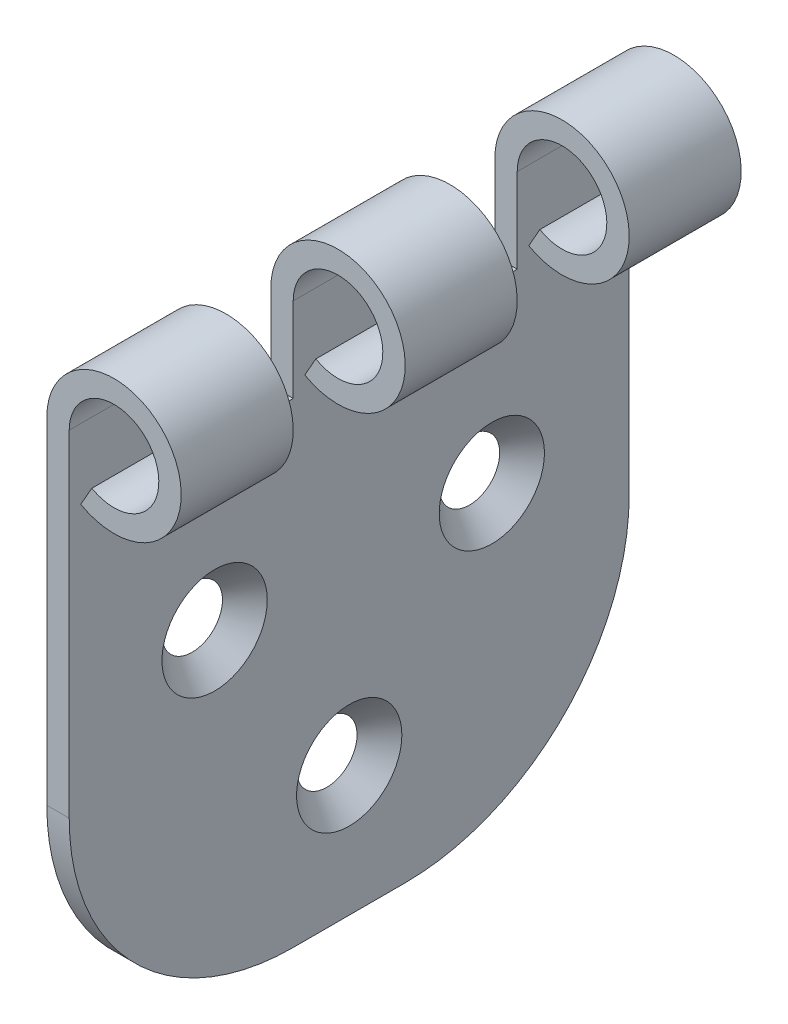
SolidWorks part; units mm, degrees
ref_plane "Front Plane" through (0, 0, 0) normal (0, 0, 1) x (1, 0, 0)
ref_plane "Top Plane" through (0, 0, 0) normal (0, 1, 0) x (1, 0, 0)
ref_plane "Right Plane" through (0, 0, 0) normal (1, 0, 0) x (0, 0, -1)
sketch "Sketch1" plane through (0, 0, 0) normal (0, 0, 1) x (1, 0, 0)
  line L0 (0, 0) -> (0, 50)
  line L1 (0, 50) -> (2, 50) construction
  line L2 (2, 50) -> (2, 0)
  line L3 (2, 0) -> (0, 0)
  line L4 (3.0328, 44.7851) -> (4.0218, 46.5234)
  arc A0 (3.0328, 44.7851) -> (0, 50) centre (6, 50) ccw
  arc A1 (4.0218, 46.5234) -> (2, 50) centre (6, 50) ccw
  dimension "D3" = 12
  dimension "D1" = 50
  dimension "D2" = 2
extrude "Boss-Extrude1" add sketch "Sketch1" along normal mid plane 50
sketch "Sketch2" plane through (2, 0, 0) normal (1, 0, 0) x (0, 0, -1)
  line L0 (-25, 0) -> (-25, 50) construction
  line L1 (-15, 63.0451) -> (-5, 63.0451)
  line L2 (-15, 63.0451) -> (-15, 42.4547)
  line L3 (-15, 42.4547) -> (-5, 42.4547)
  line L4 (-5, 63.0451) -> (-5, 42.4547)
  line L9 (5, 63.0451) -> (15, 63.0451)
  line L10 (5, 63.0451) -> (5, 42.4547)
  line L11 (5, 42.4547) -> (15, 42.4547)
  line L12 (15, 63.0451) -> (15, 42.4547)
  dimension "D1" = 10
  dimension "D2" = 10
  dimension "D3" = 10
  dimension "D4" = 10
extrude "Cut-Extrude1" cut sketch "Sketch2" along normal through all both and the other way through all
fillet "Fillet1" radius 20 2 edges at (1, 0, -25) (1, 0, 25)
hole_wizard "CSK for M4 Countersunk Flat Head Screw1" positions "Sketch3" profile "Sketch4" countersink size "M4" standard "ISO" end condition through all
sketch "Sketch3" plane through (2, 0, 0) normal (1, 0, 0) x (0, 0, -1)
  point P0 (0, 11.5875)
  point P2 (-12.0173, 28.0398)
  point P4 (12.7326, 27.0383)
sketch "Sketch4" plane through (2, 11.5875, 0) normal (0, 1, 0) x (0, 0, -1)
  line L0 (0, 0) -> (0, 2)
  line L1 (0, 2) -> (2.25, 2)
  line L2 (2.25, 2) -> (2.25, 2.45)
  line L3 (2.25, 2.45) -> (4.7, 0)
  line L5 (4.7, 0) -> (0, 0)
  line L6 (-2.25, 2.45) -> (-4.7, 0) construction
  line L11 (0, -6.35) -> (0, 107.95) construction
  dimension "Thru Hole Dia." = 4.5
  dimension "Thru Hole Depth" = 2
  dimension "Near C'Sink Dia." = 9.4
  dimension "Near C'Sink Angle" = 90
